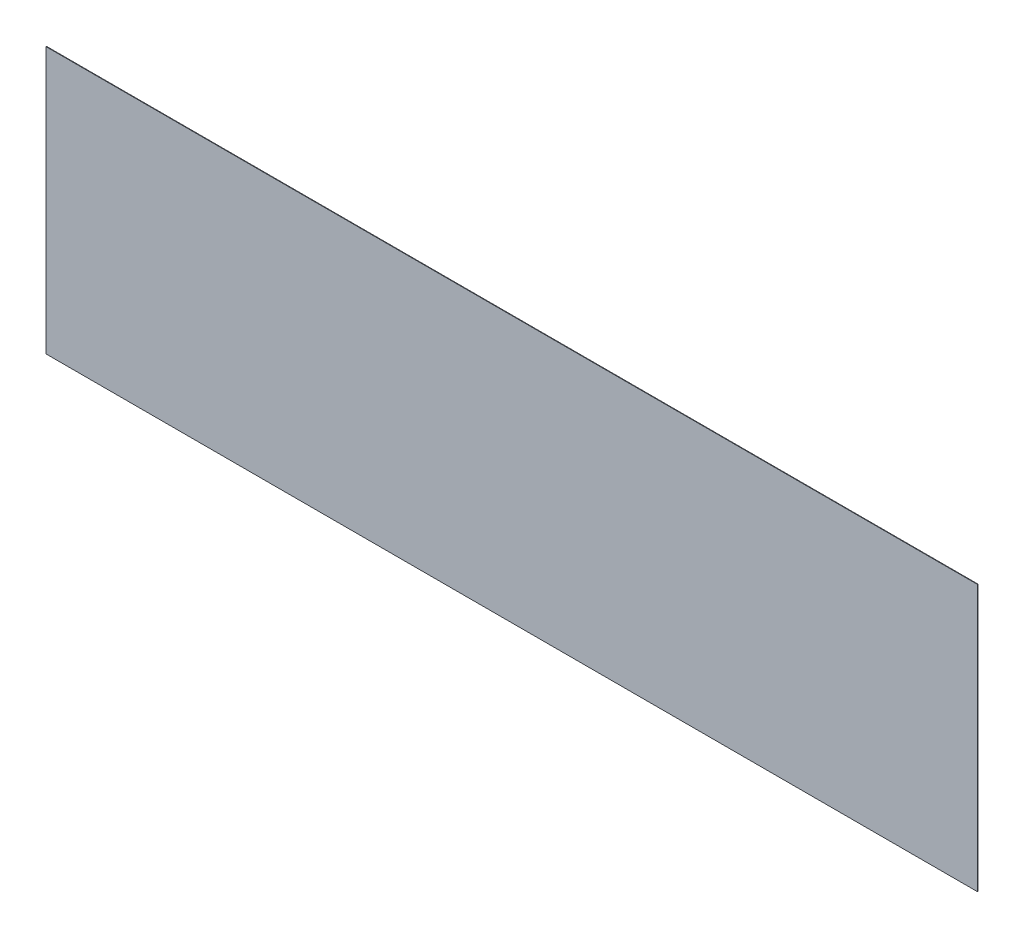
SolidWorks part; units mm, degrees
ref_plane "Front Plane" through (0, 0, 0) normal (0, 0, 1) x (1, 0, 0)
ref_plane "Top Plane" through (0, 0, 0) normal (0, 1, 0) x (1, 0, 0)
ref_plane "Right Plane" through (0, 0, 0) normal (1, 0, 0) x (0, 0, -1)
sketch "Sketch1" plane through (0, 0, 0) normal (0, 0, 1) x (1, 0, 0)
  line L1 (-26.9715, 14.4303) -> (43.0285, 14.4303)
  line L2 (-26.9715, 14.4303) -> (-26.9715, -5.5697)
  line L3 (-26.9715, -5.5697) -> (43.0285, -5.5697)
  line L4 (43.0285, 14.4303) -> (43.0285, -5.5697)
  dimension "D1" = 70
  dimension "D2" = 20
extrude "Boss-Extrude1" add sketch "Sketch1" along normal blind 0.04
